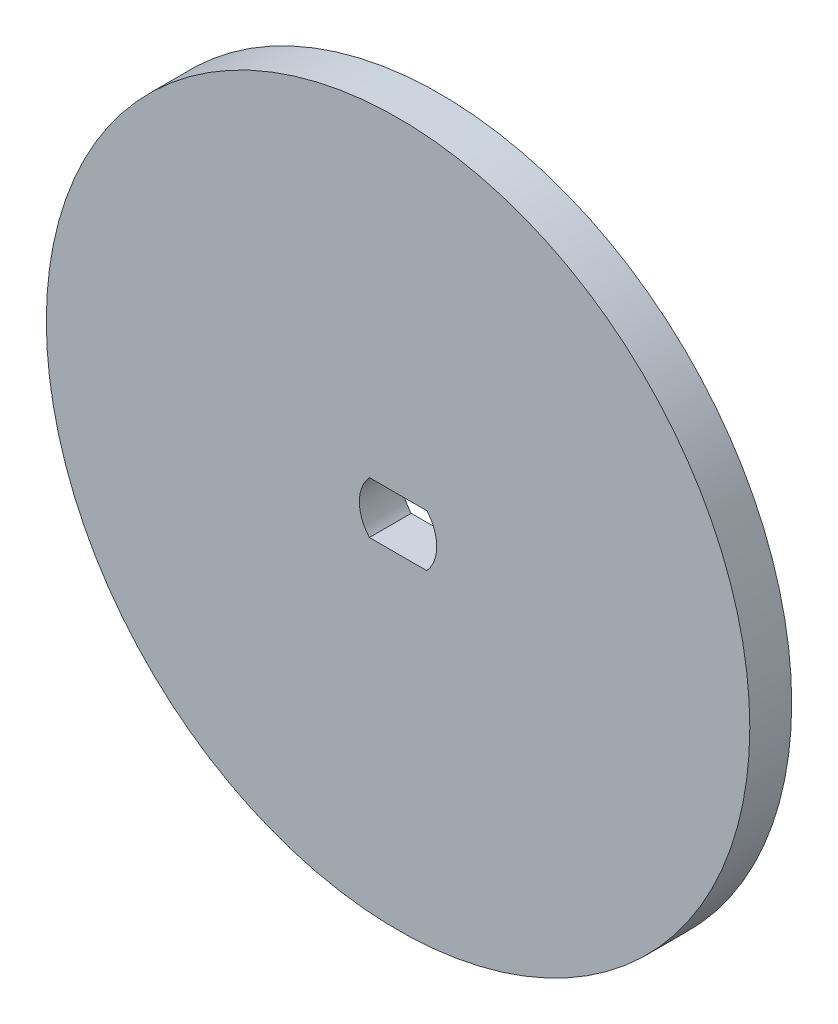
SolidWorks part; units mm, degrees
ref_plane "Front Plane" through (0, 0, 0) normal (0, 0, 1) x (1, 0, 0)
ref_plane "Top Plane" through (0, 0, 0) normal (0, 1, 0) x (1, 0, 0)
ref_plane "Right Plane" through (0, 0, 0) normal (1, 0, 0) x (0, 0, -1)
sketch "Sketch1" plane through (0, 0, 0) normal (0, 0, 1) x (1, 0, 0)
  line L1 (-2.1752, 1.9685) -> (2.1752, 1.9685)
  line L2 (-2.1752, 1.9685) -> (-2.1752, -1.9685)
  line L3 (-2.1752, -1.9685) -> (2.1752, -1.9685)
  line L4 (2.1752, 1.9685) -> (2.1752, -1.9685)
  circle A0 centre (0, 0) radius 26.67
  arc A1 (2.1752, -1.9685) -> (2.1752, 1.9685) centre (0, 0) ccw
  arc A2 (-2.1752, 1.9685) -> (-2.1752, -1.9685) centre (0, 0) ccw
  dimension "D1" = 53.34
  dimension "D2" = 2.9337
  dimension "D3" = 3.937
extrude "Boss-Extrude1" add sketch "Sketch1" along normal blind 3.175 contours A0 A2 L1 A1 L3
